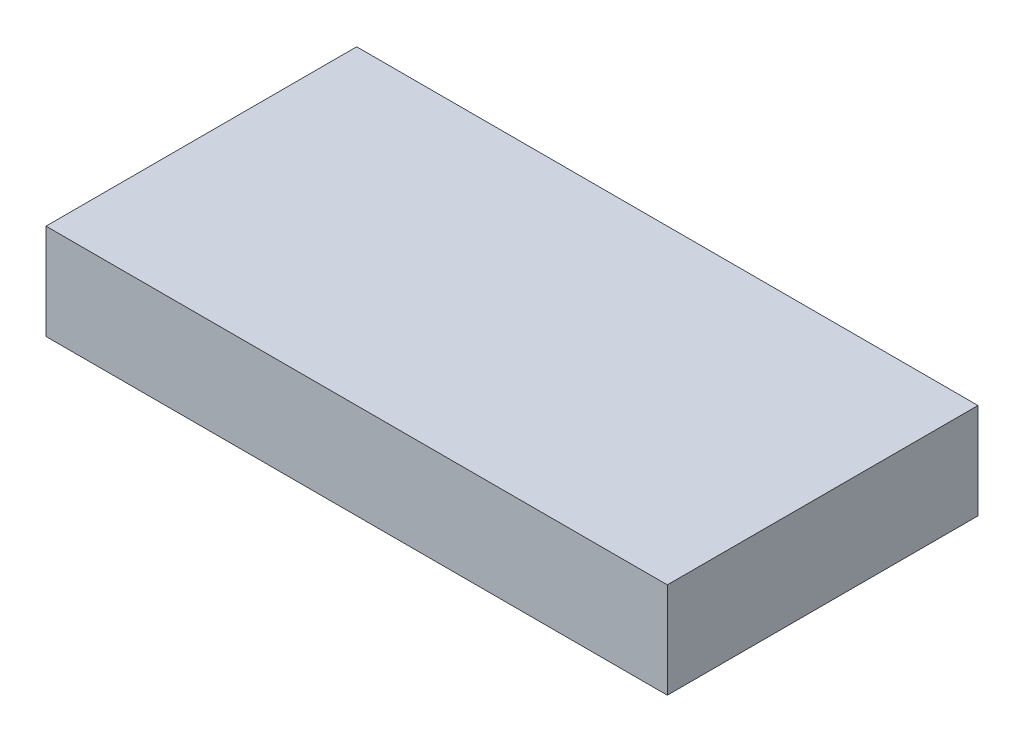
SolidWorks part; units mm, degrees
ref_plane "Front Plane" through (0, 0, 0) normal (0, 0, 1) x (1, 0, 0)
ref_plane "Top Plane" through (0, 0, 0) normal (0, 1, 0) x (1, 0, 0)
ref_plane "Right Plane" through (0, 0, 0) normal (1, 0, 0) x (0, 0, -1)
sketch "Sketch1" plane through (0, 0, 0) normal (0, 1, 0) x (1, 0, 0)
  line L1 (0, 0) -> (130, 0)
  line L2 (0, 0) -> (0, 65)
  line L3 (0, 65) -> (130, 65)
  line L4 (130, 0) -> (130, 65)
  dimension "D1" = 130
  dimension "D2" = 65
extrude "Boss-Extrude1" add sketch "Sketch1" along normal blind 20
